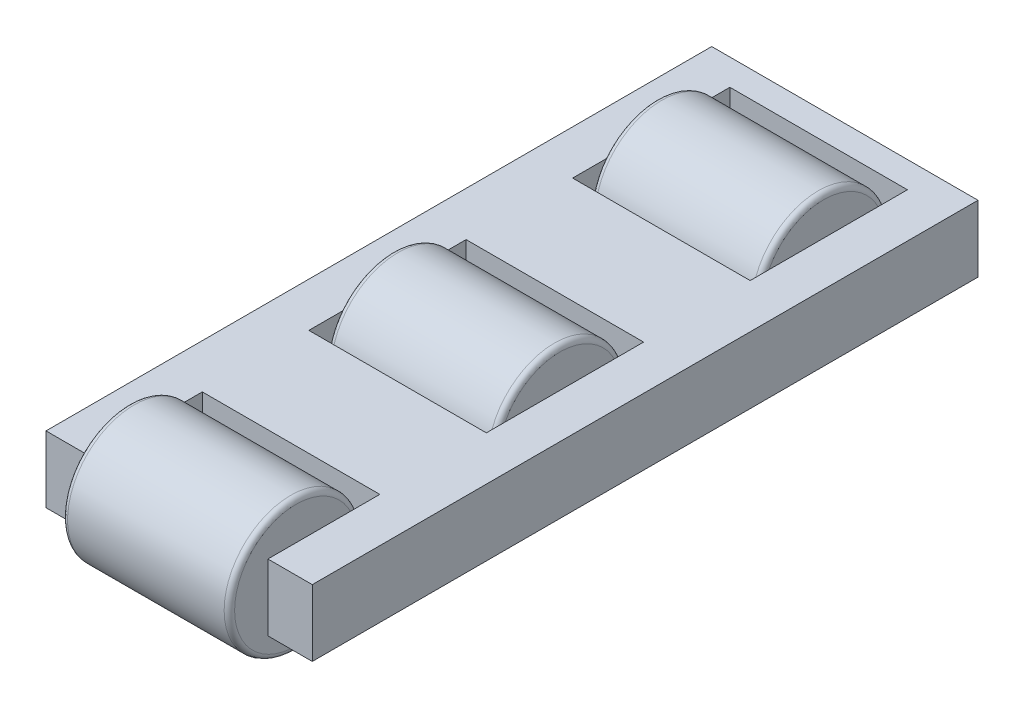
SolidWorks part; units mm, degrees
ref_plane "Front Plane" through (0, 0, 0) normal (0, 0, 1) x (1, 0, 0)
ref_plane "Top Plane" through (0, 0, 0) normal (0, 1, 0) x (1, 0, 0)
ref_plane "Right Plane" through (0, 0, 0) normal (1, 0, 0) x (0, 0, -1)
sketch "Sketch1" plane through (0, 0, 0) normal (0, 1, 0) x (1, 0, 0)
  line L1 (-25.4, -63.5) -> (25.4, -63.5)
  line L2 (-25.4, -63.5) -> (-25.4, 63.5)
  line L3 (-25.4, 63.5) -> (25.4, 63.5)
  line L4 (25.4, -63.5) -> (25.4, 63.5)
  line L5 (-25.4, -63.5) -> (25.4, 63.5) construction
  line L6 (-25.4, 63.5) -> (25.4, -63.5) construction
  point P0 (0, 0)
  dimension "D1" = 127
  dimension "D2" = 50.8
extrude "Boss-Extrude1" add sketch "Sketch1" along normal blind 12.7
sketch "Sketch2" plane through (25.4, 0, 0) normal (1, 0, 0) x (0, 0, -1)
  line L0 (-63.5, 12.7) -> (63.5, 12.7) construction
  line L1 (-63.5, 0) -> (-50.8, 0) construction
  line L2 (-63.5, 0) -> (-63.5, 12.7) construction
  line L3 (-63.5, 12.7) -> (-50.8, 12.7) construction
  line L4 (-50.8, 0) -> (-50.8, 12.7) construction
  line L5 (-63.5, 0) -> (-50.8, 12.7) construction
  line L6 (43.5, 9.8912) -> (63.5, 9.8912) construction
  line L7 (63.5, 12.7) -> (63.5, 0) construction
  line L8 (-57.15, 9.8912) -> (-77.15, 9.8912) construction
  line L9 (-6.825, 12.7) -> (-6.825, 0) construction
  line L10 (-63.5, 0) -> (63.5, 0) construction
  line L11 (43.5, 12.7) -> (43.5, 0) construction
  line L12 (-57.15, 6.35) -> (-6.825, 6.35) construction
  line L13 (-6.825, 6.35) -> (43.5, 6.35) construction
  circle A0 centre (-6.825, 6.35) radius 12.7
  circle A1 centre (43.5, 6.35) radius 12.7
  circle A2 centre (-57.15, 6.35) radius 12.7
  point P13 (-6.825, 6.35)
  point P14 (43.5, 6.35)
  point P18 (-57.15, 6.35)
  dimension "D1" = 25.4
  dimension "D2" = 20
sketch "Sketch3" plane through (0, 12.7, 0) normal (0, 1, 0) x (1, 0, 0)
  line L0 (-25.4, -63.5) -> (-12.7, -63.5) construction
  line L1 (-25.4, -63.5) -> (25.4, -63.5) construction
  line L2 (-12.7, -63.5) -> (0, -63.5) construction
  line L3 (0, -63.5) -> (12.7, -63.5) construction
  line L4 (12.7, -63.5) -> (25.4, -63.5) construction
  line L5 (-25.4, -63.5) -> (-16.9333, -63.5) construction
  line L6 (-16.9333, -63.5) -> (-8.4667, -63.5) construction
  line L7 (-8.4667, -63.5) -> (0, -63.5) construction
  line L8 (0, -63.5) -> (8.4667, -63.5) construction
  line L9 (8.4667, -63.5) -> (16.9333, -63.5) construction
  line L10 (16.9333, -63.5) -> (25.4, -63.5) construction
  line L11 (-16.9333, -63.5) -> (-16.9333, -42.15)
  line L12 (16.9333, -63.5) -> (16.9333, -42.15)
  line L13 (16.9333, -42.15) -> (-16.9333, -42.15)
  line L14 (-16.9333, -63.5) -> (16.9333, -63.5)
  line L15 (-16.9333, 8.175) -> (16.9333, 8.175)
  line L16 (-16.9333, 8.175) -> (-16.9333, -21.825)
  line L17 (-16.9333, -21.825) -> (16.9333, -21.825)
  line L18 (16.9333, 8.175) -> (16.9333, -21.825)
  line L19 (16.9333, 28.5) -> (-16.9333, 28.5)
  line L20 (16.9333, 28.5) -> (16.9333, 58.5)
  line L21 (16.9333, 58.5) -> (-16.9333, 58.5)
  line L22 (-16.9333, 28.5) -> (-16.9333, 58.5)
  point P30 (16.9333, -6.825)
  point P32 (16.9333, 43.5)
  dimension "D1" = 15
  dimension "D2" = 30
extrude "Cut-Extrude1" cut sketch "Sketch3" against normal up to surface (12.7 mm away) up to face at (0, 0, 0)
sketch "Sketch4" plane through (0, 12.7, 0) normal (0, 1, 0) x (1, 0, 0)
  line L0 (12.5526, 28.5) -> (12.5526, 8.175) construction
  line L1 (-16.9333, 28.5) -> (16.9333, 28.5) construction
  line L2 (16.9333, 8.175) -> (-16.9333, 8.175) construction
  line L4 (-17.78, 5.6375) -> (-25.4, 5.6375)
  line L5 (-17.78, 5.6375) -> (-17.78, 31.0375)
  line L6 (-17.78, 31.0375) -> (-25.4, 31.0375)
  line L7 (-25.4, 5.6375) -> (-25.4, 31.0375)
  line L8 (-17.78, 5.6375) -> (-25.4, 31.0375) construction
  line L9 (-17.78, 31.0375) -> (-25.4, 5.6375) construction
  line L10 (9.0274, -21.825) -> (9.0274, -42.15) construction
  line L11 (-25.4, -44.6875) -> (-17.78, -44.6875)
  line L12 (-25.4, -44.6875) -> (-25.4, -19.2875)
  line L13 (-25.4, -19.2875) -> (-17.78, -19.2875)
  line L14 (-17.78, -44.6875) -> (-17.78, -19.2875)
  line L15 (-25.4, -44.6875) -> (-17.78, -19.2875) construction
  line L16 (-25.4, -19.2875) -> (-17.78, -44.6875) construction
  line L17 (-16.9333, -21.825) -> (16.9333, -21.825) construction
  line L18 (16.9333, -42.15) -> (-16.9333, -42.15) construction
  line L20 (-25.4, 63.5) -> (-25.4, -63.5) construction
  point P6 (9.0274, -31.9875)
  point P7 (-21.59, 18.3375)
  point P12 (12.5526, 18.3375)
  point P16 (-21.59, -31.9875)
  dimension "D1" = 7.62
  dimension "D2" = 25.4
ref_plane "Plane1" through (15.9333, 0, 0) normal (-1, 0, 0) x (0, 0, 1)
ref_plane "Plane2" through (-15.9333, 0, 0) normal (1, 0, 0) x (0, 0, -1)
sketch "Sketch5" plane through (15.9333, 0, 0) normal (-1, 0, 0) x (0, 0, 1)
  circle A0 centre (6.825, 6.35) radius 12.7
  circle A1 centre (6.825, 6.35) radius 12.7 construction
  circle A2 centre (-43.5, 6.35) radius 12.7
  circle A3 centre (57.15, 6.35) radius 12.7
extrude "Boss-Extrude2" add sketch "Sketch5" along normal up to surface (31.8667 mm away) separate body up to plane "Plane2"
fillet "Fillet1" radius 1 2 edges at (-15.9333, 6.35, -5.875) (15.9333, 6.35, 19.525)
fillet "Fillet2" radius 1 2 edges at (15.9333, 6.35, -30.8) (-15.9333, 6.35, -56.2)
fillet "Fillet3" radius 1 2 edges at (15.9333, 6.35, 69.85) (-15.9333, 6.35, 44.45)
